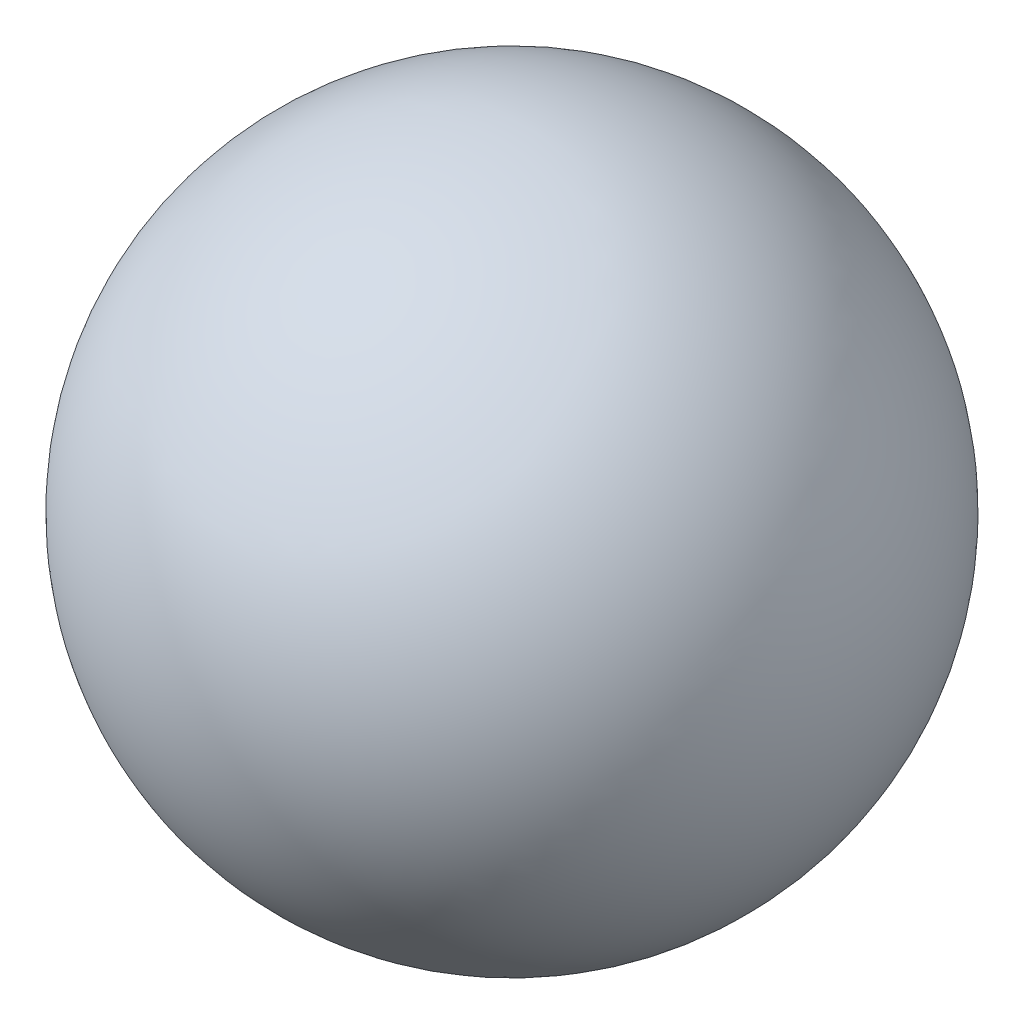
SolidWorks part; units mm, degrees
material "Silicon Rubber"
ref_plane "Front Plane" through (0, 0, 0) normal (0, 0, 1) x (1, 0, 0)
ref_plane "Top Plane" through (0, 0, 0) normal (0, 1, 0) x (1, 0, 0)
ref_plane "Right Plane" through (0, 0, 0) normal (1, 0, 0) x (0, 0, -1)
sketch "Sketch2" plane through (0, 0, 0) normal (0, 1, 0) x (1, 0, 0)
  line L0 (0, 0) -> (0, 20)
  line L1 (0, 0) -> (0, -20)
  arc A0 (0, 20) -> (0, -20) centre (0, 0) ccw
  dimension "D1" = 20
revolve "Revolve1" add sketch "Sketch2" angle 360 about L1
